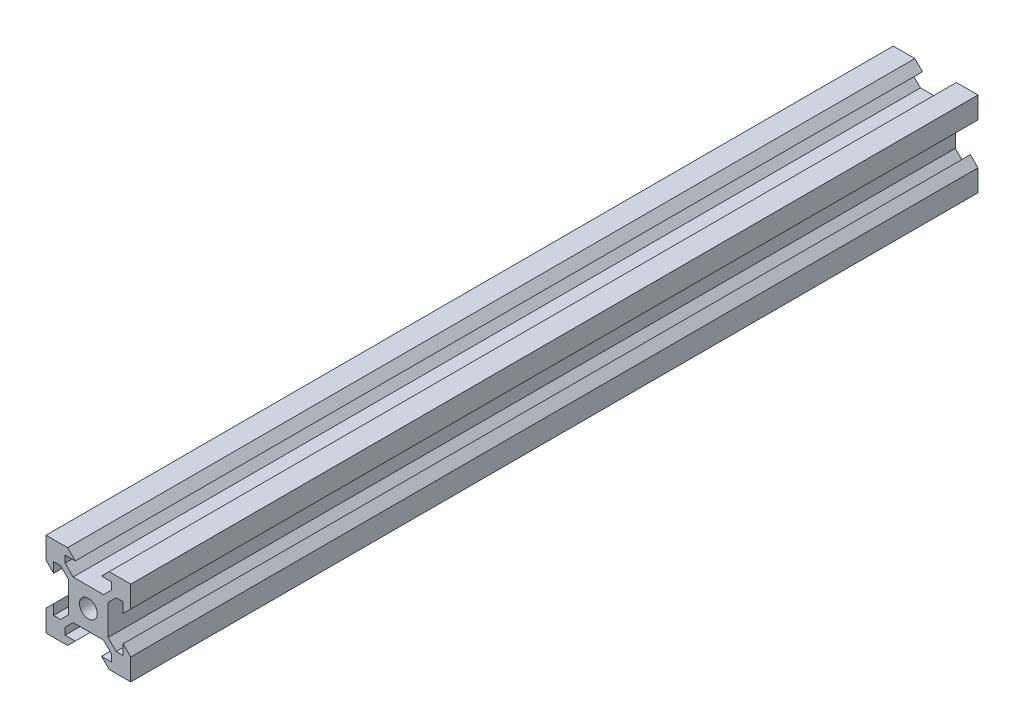
SolidWorks part; units mm, degrees
material "6063-T5"
ref_plane "Front Plane" through (0, 0, 0) normal (0, 0, 1) x (1, 0, 0)
ref_plane "Top Plane" through (0, 0, 0) normal (0, 1, 0) x (1, 0, 0)
ref_plane "Right Plane" through (0, 0, 0) normal (1, 0, 0) x (0, 0, -1)
sketch "Sketch1" plane through (0, 0, 0) normal (0, 0, 1) x (1, 0, 0)
  line L0 (3.59, 4.6507) -> (-3.59, 4.6507)
  line L5 (-10, -10) -> (10, -10)
  line L6 (-10, -10) -> (-10, 10)
  line L7 (-10, 10) -> (10, 10)
  line L8 (10, -10) -> (10, 10)
  line L9 (-10, -10) -> (10, 10) construction
  line L10 (-10, 10) -> (10, -10) construction
  line L11 (0, 10) -> (0, -10) construction
  line L12 (10, 0) -> (-10, 0) construction
  line L13 (-3.59, 4.6507) -> (-5.4993, 6.56)
  line L14 (-5.4993, 6.56) -> (-5.4993, 8.2)
  line L15 (3.59, 4.6507) -> (5.4993, 6.56)
  line L16 (5.4993, 6.56) -> (5.4993, 8.2)
  line L17 (5.4993, 8.2) -> (3.1, 8.2)
  line L18 (3.1, 8.2) -> (4.9, 10)
  line L19 (-5.4993, 8.2) -> (-3.1, 8.2)
  line L20 (-3.1, 8.2) -> (-4.9, 10)
  line L21 (3.1, -8.2) -> (4.9, -10)
  line L22 (5.4993, -8.2) -> (3.1, -8.2)
  line L23 (5.4993, -6.56) -> (5.4993, -8.2)
  line L24 (3.59, -4.6507) -> (5.4993, -6.56)
  line L25 (3.59, -4.6507) -> (-3.59, -4.6507)
  line L26 (-3.59, -4.6507) -> (-5.4993, -6.56)
  line L27 (-5.4993, -6.56) -> (-5.4993, -8.2)
  line L28 (-5.4993, -8.2) -> (-3.1, -8.2)
  line L29 (-3.1, -8.2) -> (-4.9, -10)
  line L30 (8.2, 3.1) -> (10, 4.9)
  line L31 (8.2, 3.1) -> (8.2, 5.4993)
  line L32 (8.2, 5.4993) -> (6.56, 5.4993)
  line L33 (4.6507, 3.59) -> (6.56, 5.4993)
  line L34 (4.6507, 3.59) -> (4.6507, -3.59)
  line L35 (4.6507, -3.59) -> (6.56, -5.4993)
  line L36 (8.2, -5.4993) -> (6.56, -5.4993)
  line L37 (8.2, -3.1) -> (8.2, -5.4993)
  line L38 (8.2, -3.1) -> (10, -4.9)
  line L39 (-8.2, -3.1) -> (-10, -4.9)
  line L40 (-8.2, -3.1) -> (-8.2, -5.4993)
  line L41 (-8.2, -5.4993) -> (-6.56, -5.4993)
  line L42 (-4.6507, -3.59) -> (-6.56, -5.4993)
  line L43 (-4.6507, 3.59) -> (-4.6507, -3.59)
  line L44 (-4.6507, 3.59) -> (-6.56, 5.4993)
  line L45 (-8.2, 5.4993) -> (-6.56, 5.4993)
  line L46 (-8.2, 3.1) -> (-8.2, 5.4993)
  line L47 (-8.2, 3.1) -> (-10, 4.9)
  line L48 (4.9, 10) -> (-4.9, 10)
  line L49 (-10, 4.9) -> (-10, -4.9)
  line L50 (10, -4.9) -> (10, 4.9)
  line L51 (4.9, -10) -> (-4.9, -10)
  circle A1 centre (0, 0) radius 2.1
  point P11 (0, 4.6507)
  point P35 (4.6507, 0)
  dimension "D1" = 4.2
  dimension "D2" = 20
  dimension "D3" = 20
  dimension "D4" = 0.75
  dimension "D5" = 3.59
  dimension "D6" = 3.1
  dimension "D7" = 1.8
  dimension "D8" = 1.64
  dimension "D9" = 3.59
  dimension "D10" = 1.64
  dimension "D11" = 1.8
  dimension "D12" = 45
  dimension "D13" = 0.75
  dimension "D14" = 3.1
extrude "Boss-Extrude1" add sketch "Sketch1" along normal mid plane 200 contours L6 L5 L8 L7 | A1 | L50 L30 L31 L32 L33 L34 L35 L36 L37 L38 | L48 L20 L19 L14 L13 L0 L15 L16 L17 L18 | L49 L39 L40 L41 L42 L43 L44 L45 L46 L47 | L51 L29 L28 L27 L26 L25 L24 L23 L22 L21
